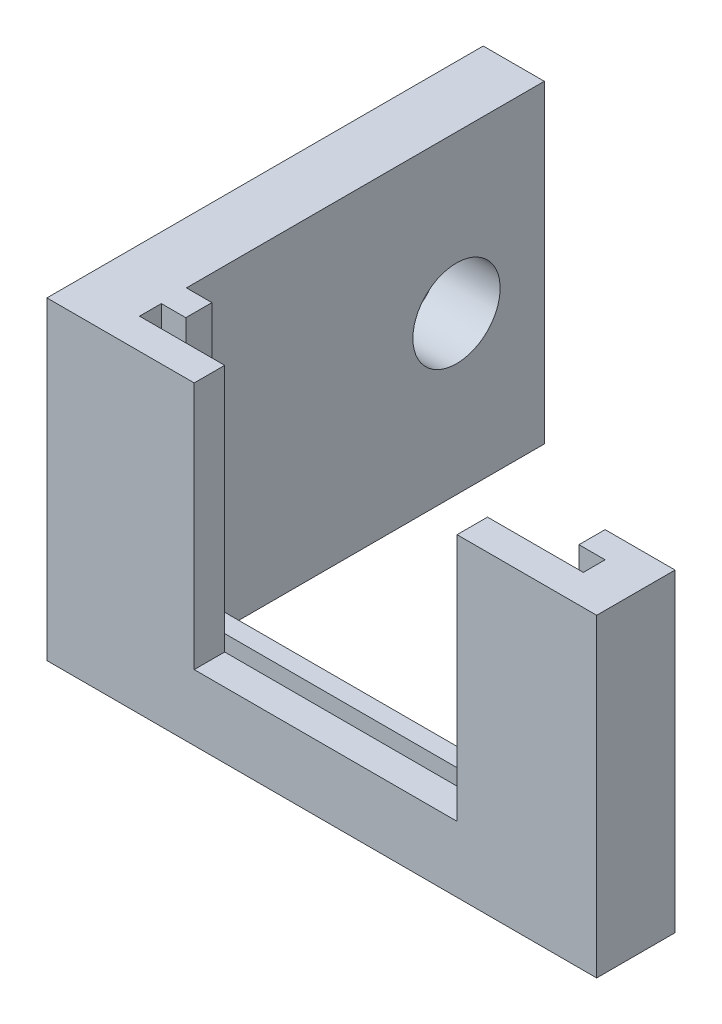
SolidWorks part; units mm, degrees
ref_plane "Спереди" through (0, 0, 0) normal (0, 0, 1) x (1, 0, 0)
ref_plane "Сверху" through (0, 0, 0) normal (0, 1, 0) x (1, 0, 0)
ref_plane "Справа" through (0, 0, 0) normal (1, 0, 0) x (0, 0, -1)
sketch "Эскиз2" plane through (0, 0, 0) normal (0, 0, 1) x (1, 0, 0)
  line L1 (0, 0) -> (3.5, 0)
  line L2 (0, 0) -> (0, 18)
  line L3 (0, 18) -> (3.5, 18)
  line L4 (3.5, 0) -> (3.5, 18)
  dimension "D1" = 3.5
  dimension "D2" = 18
extrude "Бобышка-Вытянуть1" add sketch "Эскиз2" along normal blind 25
sketch "Эскиз3" plane through (3.5, 0, 0) normal (1, 0, 0) x (0, 0, -1)
  line L0 (-25, 0) -> (0, 0) construction
  line L1 (-25, 18) -> (-20.5072, 18)
  line L2 (-25, 18) -> (-25, 0)
  line L3 (-25, 0) -> (-20.5072, 0)
  line L4 (-20.5072, 18) -> (-20.5072, 0)
extrude "Бобышка-Вытянуть2" add sketch "Эскиз3" along normal blind 28 contours L2 L1 L4 L3
sketch "Эскиз4" plane through (0, 18, 0) normal (0, 1, 0) x (1, 0, 0)
  line L0 (4.9596, -20.5072) -> (4.9596, -22.0038)
  line L1 (31.5, -20.5072) -> (3.5, -20.5072) construction
  line L2 (4.9596, -22.0038) -> (3.5596, -22.0038)
  line L3 (3.5596, -22.0038) -> (3.5596, -23.2538)
  line L4 (3.5596, -23.2538) -> (28.9896, -23.2538)
  line L5 (28.9896, -23.2538) -> (28.9896, -22.0038)
  line L6 (28.9896, -22.0038) -> (27.4896, -22.0038)
  line L7 (27.4896, -22.0038) -> (27.4896, -20.5072)
  line L8 (27.4896, -20.5072) -> (4.9596, -20.5072)
  dimension "D1" = 1.25
  dimension "D2" = 1.25
  dimension "D3" = 1.4
  dimension "D4" = 1.5
  dimension "D5" = 25.43
extrude "Вырез-Вытянуть1" cut sketch "Эскиз4" against normal blind 15
sketch "Эскиз5" plane through (0, 3, 0) normal (0, 1, 0) x (1, 0, 0)
  line L1 (6.0357, -22.684) -> (24.0357, -22.684)
  line L2 (6.0357, -22.684) -> (6.0357, -21.564)
  line L3 (6.0357, -21.564) -> (24.0357, -21.564)
  line L4 (24.0357, -22.684) -> (24.0357, -21.564)
  dimension "D1" = 1.12
  dimension "D2" = 18
extrude "Вырез-Вытянуть2" cut sketch "Эскиз5" against normal through all
sketch "Эскиз6" plane through (0, 0, 25) normal (0, 0, 1) x (1, 0, 0)
  line L0 (0, 9) -> (31.5, 9) construction
  line L1 (8.4388, 13.4331) -> (23.5, 13.4331)
  line L2 (8.4388, 13.4331) -> (8.4388, 3.7735)
  line L3 (8.4388, 3.7735) -> (23.5, 3.7735)
  line L4 (23.5, 13.4331) -> (23.5, 3.7735)
  line L5 (0, 18) -> (0, 0) construction
  line L6 (31.5, 18) -> (31.5, 0) construction
  line L7 (15.75, 18) -> (15.75, 0) construction
  line L8 (31.5, 18) -> (0, 18) construction
  line L9 (0, 0) -> (31.5, 0) construction
  point P16 (0, 0)
  dimension "D1" = 15.0612
  dimension "D2" = 8
extrude "Вырез-Вытянуть3" cut sketch "Эскиз6" against normal through all
sketch "Эскиз7" plane through (0, 0, 0) normal (-1, 0, 0) x (0, 0, 1)
  line L0 (0, 9) -> (25, 9) construction
  line L1 (0, 18) -> (0, 0) construction
  line L2 (25, 18) -> (25, 0) construction
  circle A0 centre (5.0307, 9) radius 2.5
extrude "Вырез-Вытянуть4" cut sketch "Эскиз7" against normal through all and the other way through all contours A0
sketch "Эскиз8" plane through (0, 13.4331, 0) normal (0, -1, 0) x (1, 0, 0)
  line L1 (8.4388, 23.2538) -> (23.5, 23.2538)
  line L2 (8.4388, 23.2538) -> (8.4388, 25)
  line L3 (8.4388, 25) -> (23.5, 25)
  line L4 (23.5, 23.2538) -> (23.5, 25)
extrude "Вырез-Вытянуть5" cut sketch "Эскиз8" against normal through all
